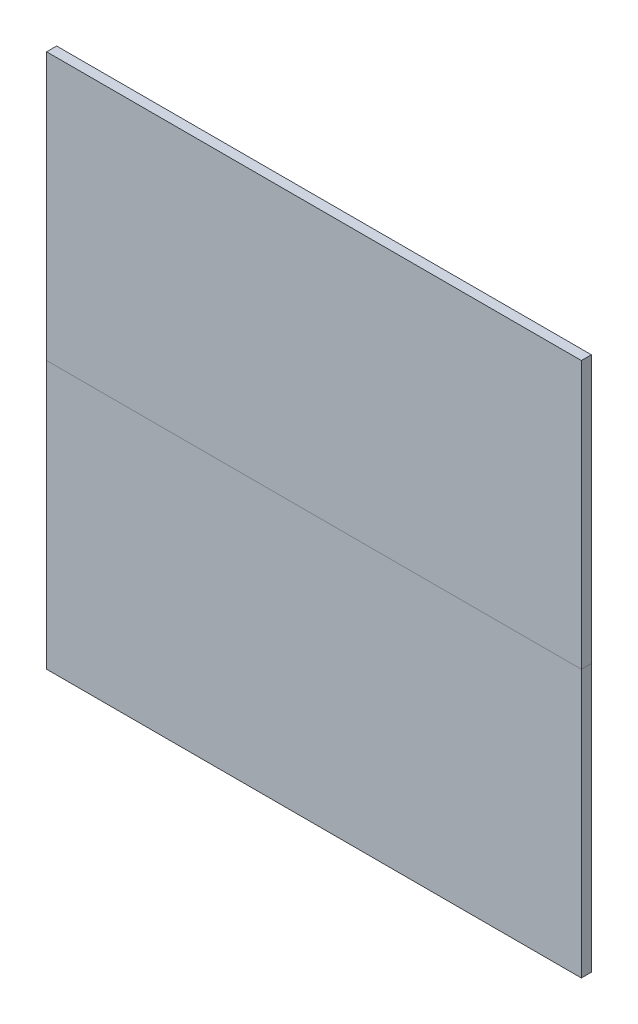
SolidWorks part; units mm, degrees
ref_plane "Alzado" through (0, 0, 0) normal (0, 0, 1) x (1, 0, 0)
ref_plane "Planta" through (0, 0, 0) normal (0, 1, 0) x (1, 0, 0)
ref_plane "Vista lateral" through (0, 0, 0) normal (1, 0, 0) x (0, 0, -1)
sketch "Croquis1" plane through (0, 0, 0) normal (0, 0, 1) x (1, 0, 0)
  line L1 (0, 0) -> (16, 0)
  line L2 (0, 0) -> (0, 8)
  line L3 (0, 8) -> (16, 8)
  line L4 (16, 0) -> (16, 8)
  dimension "D1" = 16
  dimension "D2" = 8
extrude "Saliente-Extruir1" add sketch "Croquis1" along normal blind 0.3
sketch "Croquis2" plane through (0, 0, 0.3) normal (0, 0, 1) x (1, 0, 0)
  line L0 (16, 0) -> (16, 8) construction
  line L1 (0, 8) -> (16, 8)
  line L2 (0, 8) -> (0, 16)
  line L3 (0, 16) -> (16, 16)
  line L4 (16, 8) -> (16, 16)
  line L5 (16, 8) -> (0, 8) construction
  dimension "D1" = 8
extrude "Saliente-Extruir2" add sketch "Croquis2" against normal up to surface (0.3 mm away) separate body up to face at (8, 4, 0)
